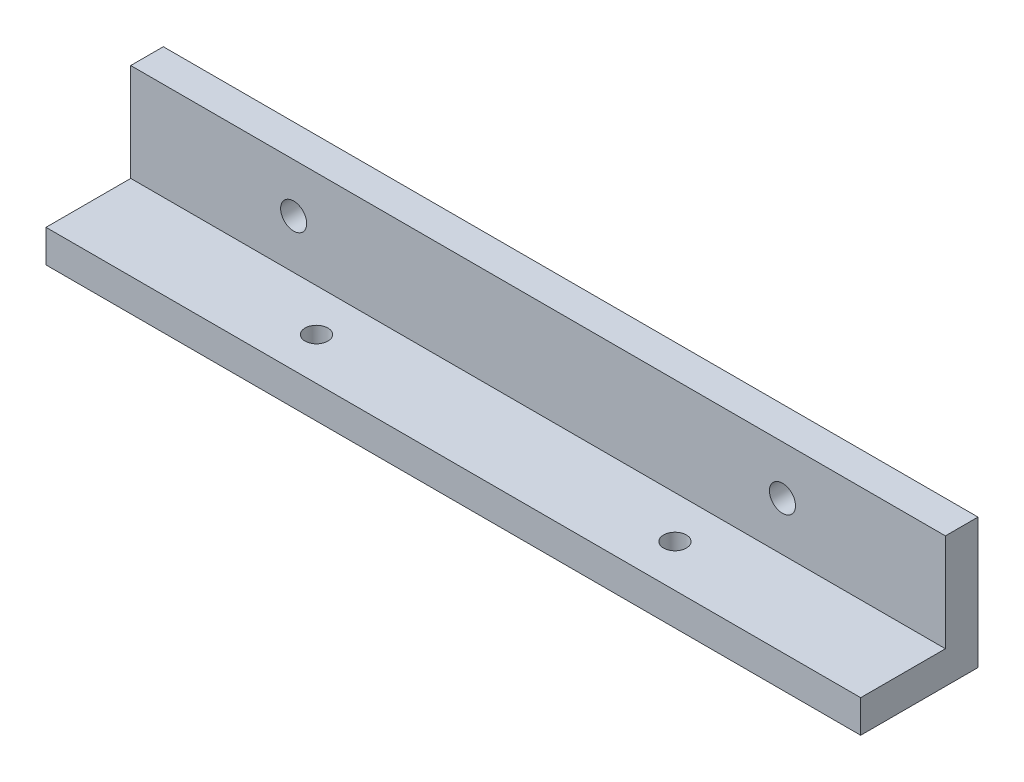
SolidWorks part; units mm, degrees
material "PET"
ref_plane "Front Plane" through (0, 0, 0) normal (0, 0, 1) x (1, 0, 0)
ref_plane "Top Plane" through (0, 0, 0) normal (0, 1, 0) x (1, 0, 0)
ref_plane "Right Plane" through (0, 0, 0) normal (1, 0, 0) x (0, 0, -1)
sketch "Sketch1" plane through (0, 0, 0) normal (0, 1, 0) x (1, 0, 0)
  line L1 (0, 0) -> (125, 0)
  line L2 (0, 0) -> (0, 18)
  line L3 (0, 18) -> (125, 18)
  line L4 (125, 0) -> (125, 18)
  dimension "D1" = 125
  dimension "D2" = 18
extrude "Boss-Extrude1" add sketch "Sketch1" against normal blind 5
sketch "Sketch3" plane through (0, 0, 0) normal (0, 1, 0) x (1, 0, 0)
  line L0 (125, 0) -> (125, 18) construction
  line L1 (0, 18) -> (125, 18)
  line L2 (0, 18) -> (0, 13)
  line L3 (0, 13) -> (125, 13)
  line L4 (125, 18) -> (125, 13)
  dimension "D1" = 5
extrude "Boss-Extrude2" add sketch "Sketch3" along normal blind 15
sketch "Sketch5" plane through (0, 0, -13) normal (0, 0, 1) x (1, 0, 0)
  line L0 (0, 15) -> (0, 0) construction
  line L1 (125, 15) -> (125, 0) construction
  line L2 (0, 0) -> (125, 0) construction
  circle A0 centre (25, 7.5) radius 2
  circle A1 centre (100, 7.5) radius 2
  dimension "D1" = 4
  dimension "D2" = 4
  dimension "D3" = 25
  dimension "D4" = 25
  dimension "D5" = 7.5
  dimension "D6" = 7.5
extrude "Cut-Extrude1" cut sketch "Sketch5" against normal through all
sketch "Sketch6" plane through (0, 0, 0) normal (0, 1, 0) x (1, 0, 0)
  line L2 (0, 13) -> (0, 0) construction
  line L3 (125, 0) -> (125, 13) construction
  line L4 (0, 0) -> (125, 0) construction
  circle A0 centre (35, 6.5) radius 1.75
  circle A1 centre (90, 6.5) radius 1.75
  dimension "D1" = 3.5
  dimension "D2" = 3.5
  dimension "D3" = 35
  dimension "D4" = 35
  dimension "D5" = 6.5
  dimension "D6" = 6.5
extrude "Cut-Extrude2" cut sketch "Sketch6" against normal through all
